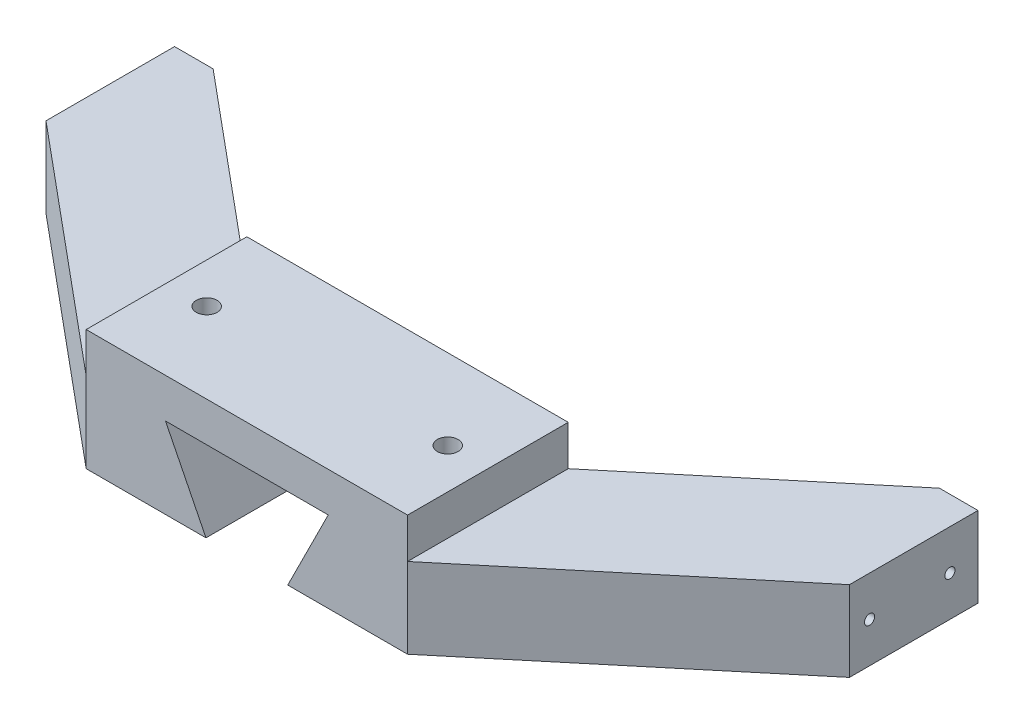
SolidWorks part; units mm, degrees
ref_plane "Front Plane" through (0, 0, 0) normal (0, 0, 1) x (1, 0, 0)
ref_plane "Top Plane" through (0, 0, 0) normal (0, 1, 0) x (1, 0, 0)
ref_plane "Right Plane" through (0, 0, 0) normal (1, 0, 0) x (0, 0, -1)
sketch "Sketch1" plane through (0, 0, 0) normal (0, 0, 1) x (1, 0, 0)
  line L1 (25.4, -9.525) -> (-25.4, -9.525)
  line L2 (25.4, -9.525) -> (25.4, 9.525)
  line L3 (25.4, 9.525) -> (-25.4, 9.525)
  line L4 (-25.4, -9.525) -> (-25.4, 9.525)
  line L5 (25.4, -9.525) -> (-25.4, 9.525) construction
  line L6 (25.4, 9.525) -> (-25.4, -9.525) construction
  point P0 (0, 0)
  dimension "D1" = 50.8
  dimension "D2" = 19.05
extrude "Boss-Extrude1" add sketch "Sketch1" along normal blind 25.4
sketch "Sketch2" plane through (0, 0, 0) normal (0, 0, -1) x (-1, 0, 0)
  line L0 (0, -9.525) -> (-6.35, -9.525) construction
  line L1 (25.4, -9.525) -> (-25.4, -9.525) construction
  line L2 (0, -9.525) -> (6.35, -9.525) construction
  line L3 (-6.35, -9.525) -> (-12.7, 3.175)
  line L4 (-12.7, 3.175) -> (12.7, 3.175)
  line L5 (12.7, 3.175) -> (6.35, -9.525)
  line L6 (-6.4394, -9.5697) -> (-12.8618, 3.275)
  line L7 (-12.8618, 3.275) -> (12.8618, 3.275)
  line L8 (12.8618, 3.275) -> (6.4394, -9.5697)
  line M9 (-25.4, -9.525) -> (25.4, -9.525)
  dimension "D1" = 6.35
  dimension "D2" = 6.35
  dimension "D3" = 6.35
  dimension "D4" = 0.1
  dimension "D5" = 12.7
extrude "Cut-Extrude1" cut sketch "Sketch2" against normal blind 38.1 and the other way through all contours L8 L7 L6 L3 L4 L5 M9 | L5 L4 L3 M9
hole_wizard "M4x0.7 Tapped Hole1" positions "Sketch3" profile "Sketch4" tap size "M4x0.7" standard "ANSI Metric"
sketch "Sketch3" plane through (0, 9.525, 0) normal (0, 1, 0) x (1, 0, 0)
  line L0 (19.05, -25.4) -> (19.05, 0) construction
  line L1 (25.4, -25.4) -> (-25.4, -25.4) construction
  line L2 (25.4, 0) -> (-25.4, 0) construction
  line L3 (-19.05, -25.4) -> (-19.05, 0) construction
  line L4 (25.4, -25.4) -> (25.4, 0) construction
  line L5 (-25.4, -25.4) -> (-25.4, 0) construction
  point P8 (19.05, -12.7)
  point P14 (-19.05, -12.7)
  dimension "D1" = 6.35
  dimension "D2" = 6.35
sketch "Sketch4" plane through (-19.05, 9.525, 12.7) normal (1, 0, 0) x (0, 0, 1)
  line L0 (0, 0) -> (0, 11.1006)
  line L1 (0, 11.1006) -> (1.65, 10.1092)
  line L2 (1.65, 10.1092) -> (1.65, 0)
  line L5 (1.65, 0) -> (0, 0)
  line L10 (0, 11.1006) -> (-1.65, 10.1092) construction
  line L11 (0, -6.35) -> (0, 107.95) construction
  dimension "Tap Drill Dia." = 3.3
  dimension "Tap Drill Depth" = 10.1092
  dimension "Drill Angle" = 118
sketch "Sketch8" plane through (0, -9.525, 0) normal (0, -1, 0) x (1, 0, 0)
  line L0 (25.4, 25.4) -> (63.5, -6.35)
  line L1 (63.5, -6.35) -> (63.5, -31.75)
  line L2 (63.5, -31.75) -> (25.4, 0)
  line L4 (25.4, 25.4) -> (25.4, 0)
  dimension "D1" = 25.4
  dimension "D2" = 38.1
  dimension "D3" = 31.75
extrude "Boss-Extrude4" add sketch "Sketch8" against normal blind 12.7
sketch "Sketch9" plane through (63.5, 0, 0) normal (1, 0, 0) x (0, 0, -1)
  line L4 (6.35, -9.525) -> (31.75, -9.525)
  line L5 (31.75, -9.525) -> (31.75, 3.175)
  line L6 (31.75, 3.175) -> (6.35, 3.175)
  line L7 (6.35, 3.175) -> (6.35, -9.525)
  line L8 (6.35, -9.525) -> (31.75, -9.525)
  line L9 (31.75, -9.525) -> (31.75, 3.175)
  line L10 (31.75, 3.175) -> (6.35, 3.175)
  line L11 (6.35, 3.175) -> (6.35, -9.525)
  dimension "D1" = 0
sketch "Sketch5" plane through (0, 9.525, 0) normal (0, 1, 0) x (1, 0, 0)
  line L0 (25.4, -12.7) -> (-25.4, -12.7) construction
  line L1 (25.4, -25.4) -> (25.4, 0) construction
  line L2 (-25.4, -25.4) -> (-25.4, 0) construction
  line L3 (25.4, -25.4) -> (-25.4, -25.4) construction
  line L4 (-12.7, 0) -> (12.7, 0)
  line L5 (-12.7, 0) -> (-12.7, -25.4)
  line L6 (-12.7, -25.4) -> (12.7, -25.4)
  line L7 (12.7, 0) -> (12.7, -25.4)
  line L8 (-12.7, 0) -> (12.7, -25.4) construction
  line L9 (-12.7, -25.4) -> (12.7, 0) construction
  circle A0 centre (0, -12.7) radius 10 construction
  dimension "D1" = 20
  dimension "D2" = 25.4
sketch "Sketch16" plane through (63.5, 0, 0) normal (1, 0, 0) x (0, 0, -1)
  line L0 (19.05, 3.175) -> (19.05, -9.525) construction
  line L4 (6.35, -9.525) -> (31.75, -9.525)
  line L5 (31.75, -9.525) -> (31.75, 3.175)
  line L6 (31.75, 3.175) -> (6.35, 3.175)
  line L7 (6.35, 3.175) -> (6.35, -9.525)
  line L8 (6.35, -9.525) -> (31.75, -9.525)
  line L9 (31.75, -9.525) -> (31.75, 3.175)
  line L10 (31.75, 3.175) -> (6.35, 3.175)
  line L11 (6.35, 3.175) -> (6.35, -9.525)
  dimension "D2" = 12.7
  dimension "D1" = 0
hole_wizard "M2x0.4 Tapped Hole1" positions "Sketch17" profile "Sketch19" tap size "M2x0.4" standard "ANSI Metric"
sketch "Sketch17" plane through (63.5, 0, 0) normal (1, 0, 0) x (0, 0, -1)
  line L9 (6.35, -9.525) -> (31.75, -9.525)
  line L10 (31.75, -9.525) -> (31.75, 3.175)
  line L11 (31.75, 3.175) -> (6.35, 3.175)
  line L12 (6.35, 3.175) -> (6.35, -9.525)
  line L13 (6.35, -9.525) -> (31.75, -9.525)
  line L14 (31.75, -9.525) -> (31.75, 3.175)
  line L15 (31.75, 3.175) -> (6.35, 3.175)
  line L16 (6.35, 3.175) -> (6.35, -9.525)
  line L17 (22.225, 3.175) -> (22.225, -9.525) construction
  line L19 (9.525, 3.175) -> (9.525, -9.525) construction
  point P7 (22.225, -3.175)
  point P37 (9.525, -3.175)
  dimension "D2" = 3.175
  dimension "D3" = 9.525
  dimension "D1" = 0
cosmetic thread "Hole Thread1" parameters "D1"=6.35, "D2"=2
cosmetic thread "Hole Thread2" parameters "D1"=6.35, "D2"=2
sketch "Sketch19" plane through (63.5, -3.175, -22.225) normal (0, 1, 0) x (0, 0, -1)
  line L0 (0, 0) -> (0, 6.8307)
  line L1 (0, 6.8307) -> (0.8, 6.35)
  line L2 (0.8, 6.35) -> (0.8, 0)
  line L5 (0.8, 0) -> (0, 0)
  line L10 (0, 6.8307) -> (-0.8, 6.35) construction
  line L11 (0, -6.35) -> (0, 107.95) construction
  dimension "Tap Drill Dia." = 1.6
  dimension "Tap Drill Depth" = 6.35
  dimension "Drill Angle" = 118
sketch "Sketch20" plane through (0, 3.175, 0) normal (0, 1, 0) x (1, 0, 0)
  line L0 (63.5, 26.67) -> (57.404, 26.67)
  line L1 (63.5, 31.75) -> (63.5, 6.35) construction
  line L2 (25.4, 0) -> (63.5, 31.75) construction
  line L7 (25.4, 0) -> (25.4, -25.4)
  line L8 (25.4, -25.4) -> (63.5, 6.35)
  line L9 (63.5, 6.35) -> (63.5, 31.75)
  line L10 (63.5, 31.75) -> (25.4, 0)
  line L11 (25.4, 0) -> (25.4, -25.4)
  line L12 (25.4, -25.4) -> (63.5, 6.35)
  line L13 (63.5, 6.35) -> (63.5, 31.75)
  line L14 (63.5, 31.75) -> (25.4, 0)
  line M8 (63.5, 6.35) -> (63.5, 31.75)
  line M9 (63.5, 31.75) -> (25.4, 0)
  dimension "D2" = 5.08
  dimension "D1" = 0
extrude "Cut-Extrude2" cut sketch "Sketch20" against normal blind 12.7 contours L0 M8 M9
mirror "Mirror1" about plane through (0, 0, 0) normal (1, 0, 0) of "Cut-Extrude2", "Boss-Extrude4", "M2x0.4 Tapped Hole1"
cosmetic thread "Hole Thread3" parameters "D1"=6.35, "D2"=2
cosmetic thread "Hole Thread4" parameters "D1"=6.35, "D2"=2
